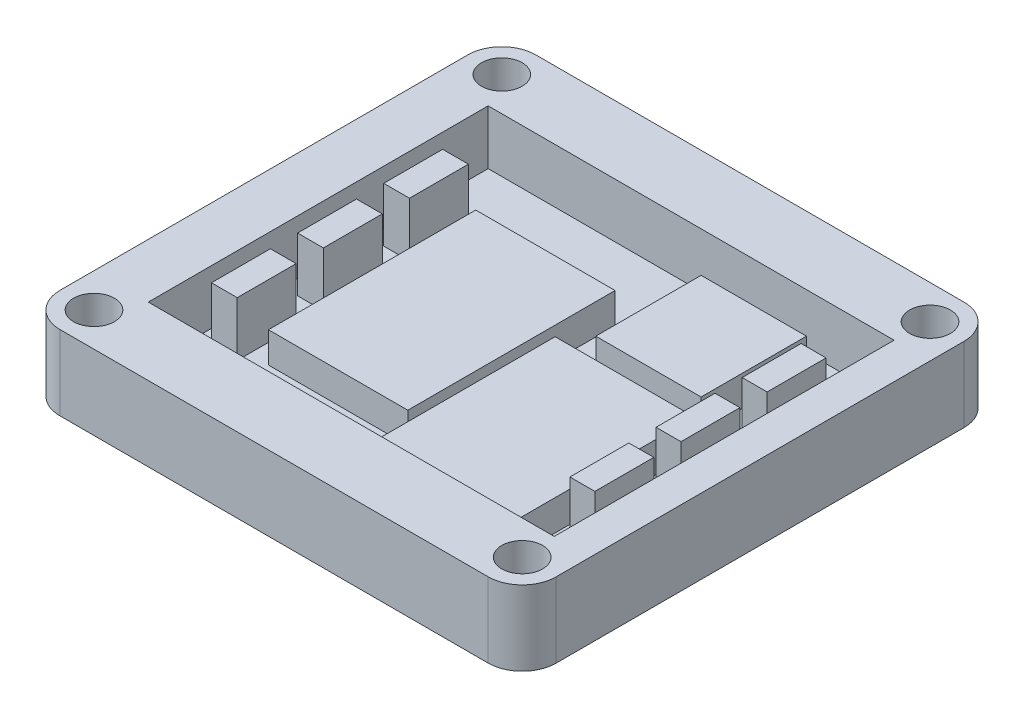
SolidWorks part; units mm, degrees
ref_plane "Front" through (0, 0, 0) normal (0, 0, 1) x (1, 0, 0)
ref_plane "Top" through (0, 0, 0) normal (0, 1, 0) x (1, 0, 0)
ref_plane "Right" through (0, 0, 0) normal (1, 0, 0) x (0, 0, -1)
sketch "Sketch2" plane through (0, 0, 0) normal (0, 1, 0) x (1, 0, 0)
  line L0 (-31.5, 35) -> (-31.5, -35) construction
  line L1 (-31.5, -35) -> (31.5, -35)
  line L2 (-36.5, -30) -> (-36.5, 30)
  line L3 (-31.5, 35) -> (31.5, 35)
  line L4 (36.5, -30) -> (36.5, 30)
  line L5 (-36.5, -35) -> (36.5, 35) construction
  line L6 (-36.5, 35) -> (36.5, -35) construction
  line L7 (-36.5, -30) -> (36.5, -30) construction
  line L8 (31.5, -35) -> (31.5, 35) construction
  line L9 (36.5, 30) -> (-36.5, 30) construction
  arc A0 (-31.5, -35) -> (-36.5, -30) centre (-31.5, -30) cw
  arc A1 (31.5, -35) -> (36.5, -30) centre (31.5, -30) ccw
  arc A2 (31.5, 35) -> (36.5, 30) centre (31.5, 30) cw
  arc A3 (-36.5, 30) -> (-31.5, 35) centre (-31.5, 30) cw
  circle A4 centre (-31.5, 30) radius 3
  circle A5 centre (-31.5, -30) radius 3
  circle A6 centre (31.5, 30) radius 3
  circle A7 centre (31.5, -30) radius 3
  point P0 (0, 0)
  dimension "D3" = 5
  dimension "D1" = 73
  dimension "D2" = 70
extrude "Boss-Extrude1" add sketch "Sketch2" along normal blind 25
sketch "Sketch5" plane through (0, 25, 0) normal (0, 1, 0) x (1, 0, 0)
  line L1 (-100, 25) -> (100, 25)
  line L2 (-100, 25) -> (-100, -25)
  line L3 (-100, -25) -> (100, -25)
  line L4 (100, 25) -> (100, -25)
  line L5 (-100, 25) -> (100, -25) construction
  line L6 (-100, -25) -> (100, 25) construction
  point P0 (0, 0)
  dimension "D1" = 200
  dimension "D2" = 50
extrude "Cut-Extrude1" cut sketch "Sketch5" against normal blind 8
sketch "Sketch8" plane through (0.0951, 17, -16.1308) normal (0, 1, 0) x (1, 0, 0)
  line L1 (20.6551, 6.4418) -> (5.1551, 6.4418)
  line L2 (20.6551, 6.4418) -> (20.6551, -9.0582)
  line L3 (20.6551, -9.0582) -> (5.1551, -9.0582)
  line L4 (5.1551, 6.4418) -> (5.1551, -9.0582)
  line L5 (20.6551, 6.4418) -> (5.1551, -9.0582) construction
  line L6 (20.6551, -9.0582) -> (5.1551, 6.4418) construction
  point P0 (12.9051, -1.3082)
  dimension "D1" = 15.5
  dimension "D2" = 15.5
sketch "Sketch9" plane through (78.1366, 17, 0) normal (0, 1, 0) x (1, 0, 0)
  line L1 (-55.305, -22.4885) -> (-75.805, -22.4885)
  line L2 (-55.305, -22.4885) -> (-55.305, 4.0115)
  line L3 (-55.305, 4.0115) -> (-75.805, 4.0115)
  line L4 (-75.805, -22.4885) -> (-75.805, 4.0115)
  line L5 (-55.305, -22.4885) -> (-75.805, 4.0115) construction
  line L6 (-55.305, 4.0115) -> (-75.805, -22.4885) construction
  point P0 (-65.555, -9.2385)
  dimension "D1" = 26.5
  dimension "D2" = 20.5
extrude "Battery" add sketch "Sketch9" along normal blind 4.5
extrude "TEG(Top Middle)" add sketch "Sketch8" along normal blind 4.5
sketch "Sketch10" plane through (-57.8748, 17, 5.9381) normal (0, 1, 0) x (1, 0, 0)
  line L1 (58.7297, -10.25) -> (38.2297, -10.25)
  line L2 (58.7297, -10.25) -> (58.7297, 20.25)
  line L3 (58.7297, 20.25) -> (38.2297, 20.25)
  line L4 (38.2297, -10.25) -> (38.2297, 20.25)
  line L5 (58.7297, -10.25) -> (38.2297, 20.25) construction
  line L6 (58.7297, 20.25) -> (38.2297, -10.25) construction
  point P0 (48.4797, 5)
  dimension "D1" = 30.5
  dimension "D2" = 20.5
extrude "PowPCB(nextbatt)" add sketch "Sketch10" along normal blind 4.5
sketch "Sketch12" plane through (0, 0, 0) normal (0, -1, 0) x (1, 0, 0)
  line L1 (-124.8645, 44.848) -> (123.0106, 44.848)
  line L2 (-124.8645, 44.848) -> (-124.8645, -57.584)
  line L3 (-124.8645, -57.584) -> (123.0106, -57.584)
  line L4 (123.0106, 44.848) -> (123.0106, -57.584)
extrude "Cut-Extrude2" cut sketch "Sketch12" against normal blind 14
sketch "Sketch13" plane through (0, 0, 25) normal (0, 0, -1) x (-1, 0, 0)
  line L0 (36.5, 17) -> (-36.5, 17) construction
  line L1 (36.5, 25) -> (28.507, 25)
  line L2 (36.5, 25) -> (36.5, 17)
  line L3 (36.5, 17) -> (28.507, 17)
  line L4 (28.507, 25) -> (28.507, 17)
  line L5 (36.5, 25) -> (-36.5, 25) construction
  line L6 (-36.5, 25) -> (-31.2104, 25)
  line L7 (-36.5, 25) -> (-36.5, 17)
  line L8 (-36.5, 17) -> (-31.2104, 17)
  line L9 (-31.2104, 25) -> (-31.2104, 17)
  point P12 (-32.1792, 25)
  point P15 (-31.2104, 25)
extrude "Boss-Extrude2" add sketch "Sketch13" along normal blind 51
sketch "Sketch14" plane through (0, 17, 0) normal (0, 1, 0) x (1, 0, 0)
  line L1 (-26.3191, -17.8951) -> (-22.5291, -17.8951)
  line L2 (-26.3191, -17.8951) -> (-26.3191, -9.2251)
  line L3 (-26.3191, -9.2251) -> (-22.5291, -9.2251)
  line L4 (-22.5291, -17.8951) -> (-22.5291, -9.2251)
  line L9 (-26.3191, 7.4449) -> (-22.5291, 7.4449)
  line L10 (-26.3191, 7.4449) -> (-26.3191, 16.1149)
  line L11 (-26.3191, 16.1149) -> (-22.5291, 16.1149)
  line L12 (-22.5291, 7.4449) -> (-22.5291, 16.1149)
  line L13 (-26.3191, -5.2251) -> (-22.5291, -5.2251)
  line L14 (-26.3191, -5.2251) -> (-26.3191, 3.4449)
  line L15 (-26.3191, 3.4449) -> (-22.5291, 3.4449)
  line L16 (-22.5291, -5.2251) -> (-22.5291, 3.4449)
  line L17 (-26.3191, -5.2251) -> (-22.5291, 3.4449) construction
  line L18 (-26.3191, 3.4449) -> (-22.5291, -5.2251) construction
  point P4 (-28.507, 0)
  point P13 (0, 0)
  point P14 (0, 0)
  point P15 (0, 0)
  point P16 (0, 0)
  point P17 (0, 0)
  point P18 (0, 0)
  point P19 (0, 0)
  point P20 (-24.4241, 3.4449)
  point P21 (-28.507, 0)
  point P22 (-24.4241, 0)
  point P24 (0, 0)
  point P25 (0, 0)
  point P26 (0, 0)
  dimension "D1" = 4
  dimension "D2" = 4
  dimension "D3" = 8.67
extrude "Boss-Extrude3" add sketch "Sketch14" along normal blind 8
sketch "Sketch15" plane through (49.4843, 25, 12.8306) normal (0, 1, 0) x (1, 0, 0)
  line L1 (-24.6911, -3.4409) -> (-21.0211, -3.4409)
  line L2 (-24.6911, -3.4409) -> (-24.6911, 5.2291)
  line L3 (-24.6911, 5.2291) -> (-21.0211, 5.2291)
  line L4 (-21.0211, -3.4409) -> (-21.0211, 5.2291)
  line L9 (-24.6911, 21.8991) -> (-21.0211, 21.8991)
  line L10 (-24.6911, 21.8991) -> (-24.6911, 30.5691)
  line L11 (-24.6911, 30.5691) -> (-21.0211, 30.5691)
  line L12 (-21.0211, 21.8991) -> (-21.0211, 30.5691)
  line L13 (-24.6911, 9.2291) -> (-21.0211, 9.2291)
  line L14 (-24.6911, 9.2291) -> (-24.6911, 17.8991)
  line L15 (-24.6911, 17.8991) -> (-21.0211, 17.8991)
  line L16 (-21.0211, 9.2291) -> (-21.0211, 17.8991)
  line L17 (-24.6911, 9.2291) -> (-21.0211, 17.8991) construction
  line L18 (-24.6911, 17.8991) -> (-21.0211, 9.2291) construction
  point P4 (-26.879, 16.1271)
  point P13 (1.628, 16.1271)
  point P14 (1.628, 16.1271)
  point P15 (1.628, 16.1271)
  point P16 (1.628, 16.1271)
  point P17 (1.628, 16.1271)
  point P18 (1.628, 16.1271)
  point P19 (1.628, 16.1271)
  point P20 (-22.8561, 17.8991)
  point P21 (-26.879, 16.1271)
  point P22 (-22.7961, 16.1271)
  point P23 (0, 0)
  point P24 (1.628, 16.1271)
  point P25 (1.628, 16.1271)
  point P26 (1.628, 16.1271)
  point P27 (0, 0)
  dimension "D1" = 4
  dimension "D2" = 4
  dimension "D3" = 8.67
  dimension "D4" = 8.67
  dimension "D5" = 8.67
extrude "Boss-Extrude4" add sketch "Sketch15" against normal blind 9
